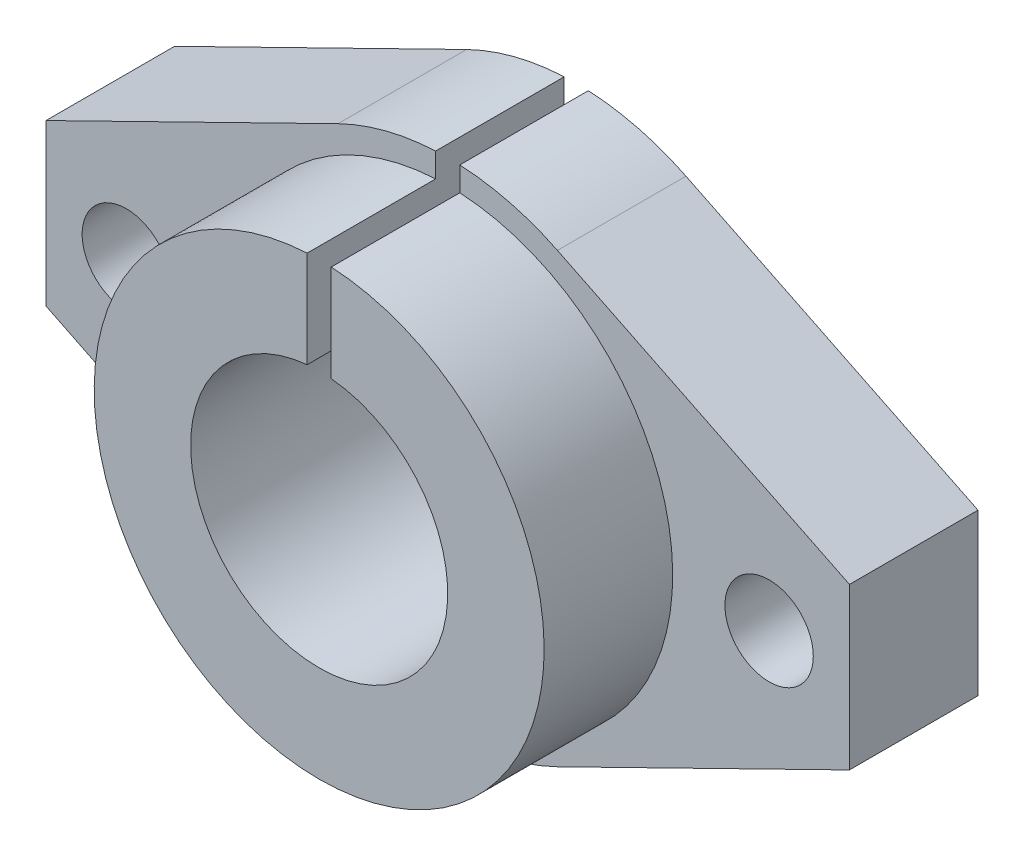
SolidWorks part; units mm, degrees
ref_plane "Front Plane" through (0, 0, 0) normal (0, 0, 1) x (1, 0, 0)
ref_plane "Top Plane" through (0, 0, 0) normal (0, 1, 0) x (1, 0, 0)
ref_plane "Right Plane" through (0, 0, 0) normal (1, 0, 0) x (0, 0, -1)
sketch "Sketch1" plane through (0, 0, 0) normal (0, 0, 1) x (1, 0, 0)
  line L0 (-6.8269, 13.9156) -> (-25, 5)
  line L1 (25, -5) -> (-25, -5) construction
  line L2 (25, -5) -> (25, 5)
  line L3 (25, 5) -> (-25, 5) construction
  line L4 (-25, -5) -> (-25, 5)
  line L5 (25, -5) -> (-25, 5) construction
  line L6 (25, 5) -> (-25, -5) construction
  line L7 (6.8269, 13.9156) -> (25, 5)
  line L8 (-6.8269, -13.9156) -> (-25, -5)
  line L9 (6.8269, -13.9156) -> (25, -5)
  arc A0 (-6.8269, -13.9156) -> (6.8269, -13.9156) centre (0, 0) ccw
  arc A2 (6.8269, 13.9156) -> (-6.8269, 13.9156) centre (0, 0) ccw
  dimension "D1" = 31
  dimension "D2" = 50
  dimension "D3" = 10
extrude "Boss-Extrude1" add sketch "Sketch1" along normal blind 8
sketch "Sketch2" plane through (0, 0, 8) normal (0, 0, 1) x (1, 0, 0)
  circle A0 centre (0, 0) radius 14
  dimension "D1" = 28
extrude "Boss-Extrude2" add sketch "Sketch2" along normal blind 8
sketch "Sketch3" plane through (0, 0, 16) normal (0, 0, 1) x (1, 0, 0)
  circle A0 centre (0, 0) radius 8
  dimension "D1" = 16
extrude "Cut-Extrude1" cut sketch "Sketch3" against normal through all
sketch "Sketch4" plane through (0, 0, 8) normal (0, 0, 1) x (1, 0, 0)
  line L0 (0, 0) -> (4.1906, 0) construction
  circle A0 centre (-20, 0) radius 2.75
  circle A1 centre (20, 0) radius 2.75
  dimension "D1" = 5.5
  dimension "D2" = 5.5
  dimension "D3" = 20
  dimension "D4" = 20
extrude "Cut-Extrude2" cut sketch "Sketch4" against normal through all
sketch "Sketch5" plane through (0, 0, 16) normal (0, 0, 1) x (1, 0, 0)
  line L0 (0, 0) -> (0, 17.7149) construction
  line L1 (-0.75, 25) -> (-0.75, 5)
  line L2 (-0.75, 25) -> (0.75, 25)
  line L3 (-0.75, 5) -> (0.75, 5)
  line L4 (0.75, 25) -> (0.75, 5)
  line L5 (-0.75, 25) -> (0.75, 5) construction
  line L6 (-0.75, 5) -> (0.75, 25) construction
  point P4 (0, 15)
  dimension "D1" = 1.5
  dimension "D2" = 20
  dimension "D3" = 15
extrude "Cut-Extrude3" cut sketch "Sketch5" against normal through all
